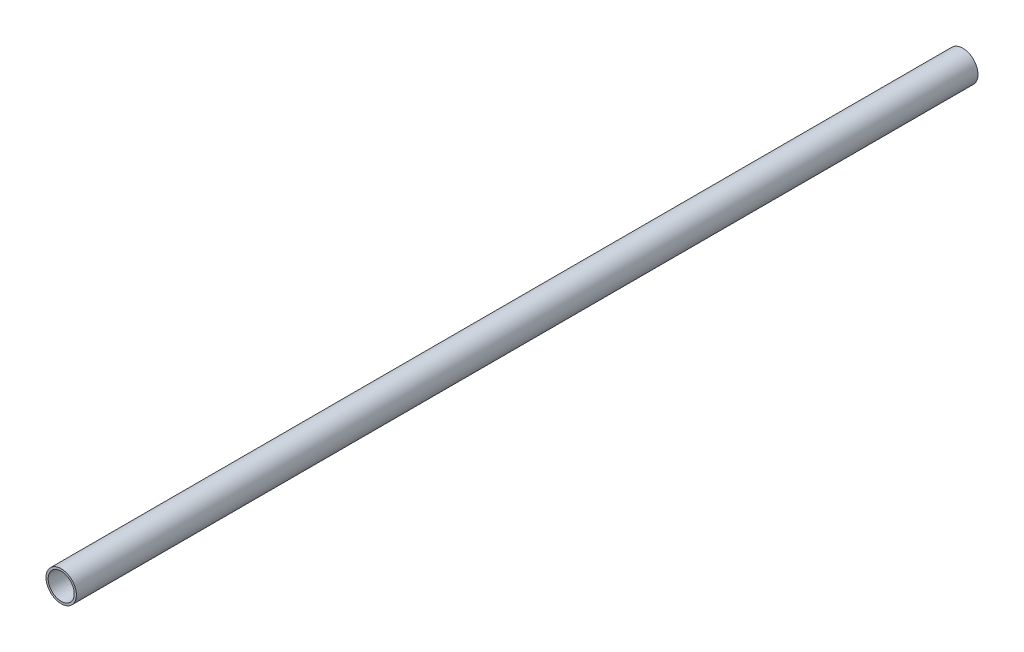
SolidWorks part; units mm, degrees
material "Thornel Mat VMA"
ref_plane "Front Plane" through (0, 0, 0) normal (0, 0, 1) x (1, 0, 0)
ref_plane "Top Plane" through (0, 0, 0) normal (0, 1, 0) x (1, 0, 0)
ref_plane "Right Plane" through (0, 0, 0) normal (1, 0, 0) x (0, 0, -1)
sketch "Sketch1" plane through (0, 0, 0) normal (0, 0, 1) x (1, 0, 0)
  circle A0 centre (0, 0) radius 7
  circle A1 centre (0, 0) radius 6
  dimension "D1" = 14
  dimension "D2" = 1
extrude "Boss-Extrude1" add sketch "Sketch1" along normal blind 415
